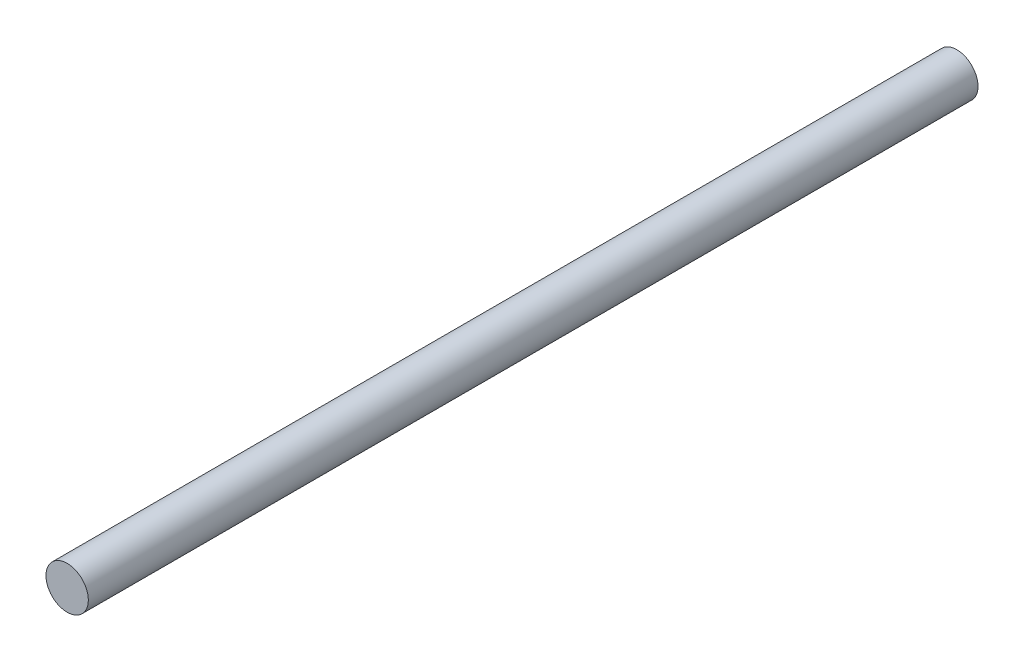
SolidWorks part; units mm, degrees
material "Thornel VCB-20 碳布"
ref_plane "前视基准面" through (0, 0, 0) normal (0, 0, 1) x (1, 0, 0)
ref_plane "上视基准面" through (0, 0, 0) normal (0, 1, 0) x (1, 0, 0)
ref_plane "右视基准面" through (0, 0, 0) normal (1, 0, 0) x (0, 0, -1)
other "Configuration Table"
sketch "草图1" plane through (0, 0, 0) normal (0, 0, 1) x (1, 0, 0)
  circle A0 centre (0, 0) radius 2
  dimension "D1" = 4
extrude "凸台-拉伸1" add sketch "草图1" along normal blind 84
